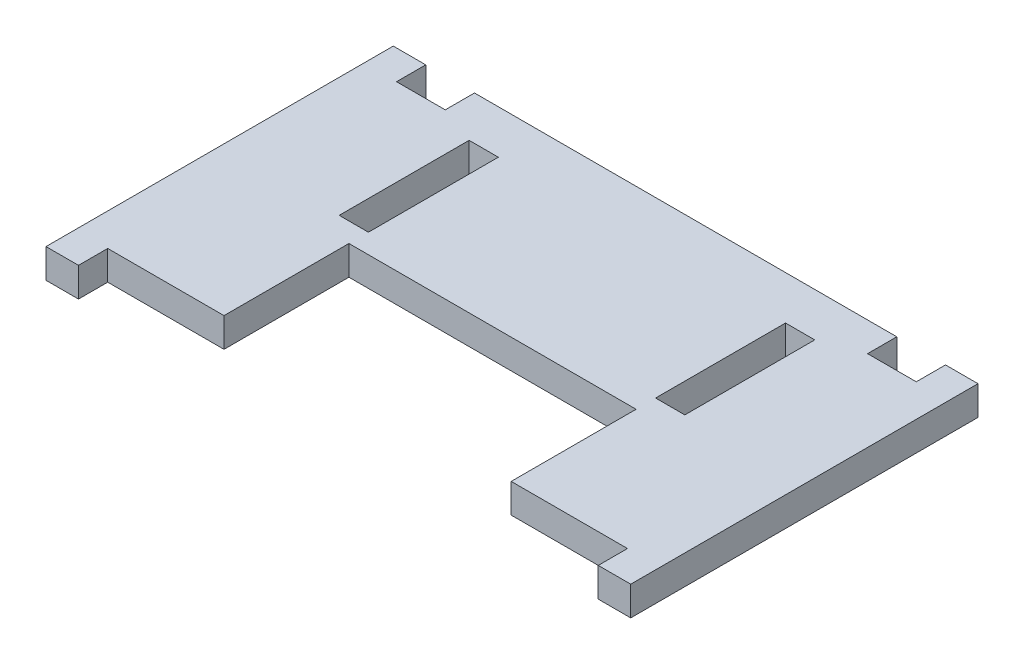
SolidWorks part; units mm, degrees
ref_plane "Front Plane" through (0, 0, 0) normal (0, 0, 1) x (1, 0, 0)
ref_plane "Top Plane" through (0, 0, 0) normal (0, 1, 0) x (1, 0, 0)
ref_plane "Right Plane" through (0, 0, 0) normal (1, 0, 0) x (0, 0, -1)
sketch "Sketch1" plane through (0, 0, 0) normal (0, 1, 0) x (1, 0, 0)
  line L0 (-40, -22.225) -> (-40, -26.725)
  line L1 (-40, 22.225) -> (0, 22.225)
  line L2 (-45, 26.725) -> (-45, -26.725)
  line L3 (-40, -22.225) -> (0, -22.225)
  line L4 (0, 22.225) -> (0, -22.225)
  line L5 (-26.6, 20) -> (-22.1, 20)
  line L6 (-26.6, 20) -> (-26.6, 0)
  line L7 (-26.6, 0) -> (-22.1, 0)
  line L8 (-22.1, 20) -> (-22.1, 0)
  line L9 (-40, -26.725) -> (-45, -26.725)
  line L10 (-40, 22.225) -> (-40, 26.725)
  line L11 (-40, 26.725) -> (-45, 26.725)
  dimension "D1" = 44.45
  dimension "D2" = 45
  dimension "D3" = 4.5
  dimension "D4" = 22.1
  dimension "D5" = 20
  dimension "D6" = 5
  dimension "D7" = 4.5
extrude "Boss-Extrude1" add sketch "Sketch1" along normal blind 4.5
mirror "Mirror1" about plane through (0, 4.5, -22.225) normal (-1, 0, 0) of "Boss-Extrude1"
sketch "Sketch2" plane through (0, 4.5, 0) normal (0, 1, 0) x (1, 0, 0)
  line L0 (-40, -22.225) -> (40, -22.225) construction
  line L1 (-22.1, -22.225) -> (22.1, -22.225)
  line L2 (-22.1, -22.225) -> (-22.1, -3)
  line L3 (-22.1, -3) -> (22.1, -3)
  line L4 (22.1, -22.225) -> (22.1, -3)
  line L5 (22.1, 0) -> (22.1, 20) construction
  line L6 (-22.1, 0) -> (-22.1, 20) construction
  dimension "D1" = 3
extrude "Cut-Extrude1" cut sketch "Sketch2" against normal through all
sketch "Sketch3" plane through (0, 4.5, 0) normal (0, 1, 0) x (1, 0, 0)
  line L0 (40, 22.225) -> (-40, 22.225) construction
  line L1 (-32.5, 22.225) -> (32.5, 22.225)
  line L2 (-32.5, 22.225) -> (-32.5, 26.725)
  line L3 (-32.5, 26.725) -> (32.5, 26.725)
  line L4 (32.5, 22.225) -> (32.5, 26.725)
  line L5 (0, 0) -> (0, 22.225) construction
  dimension "D1" = 65
  dimension "D2" = 4.5
extrude "Boss-Extrude2" add sketch "Sketch3" against normal up to surface (4.5 mm away) up to face at (0, 0, 3.1531)
